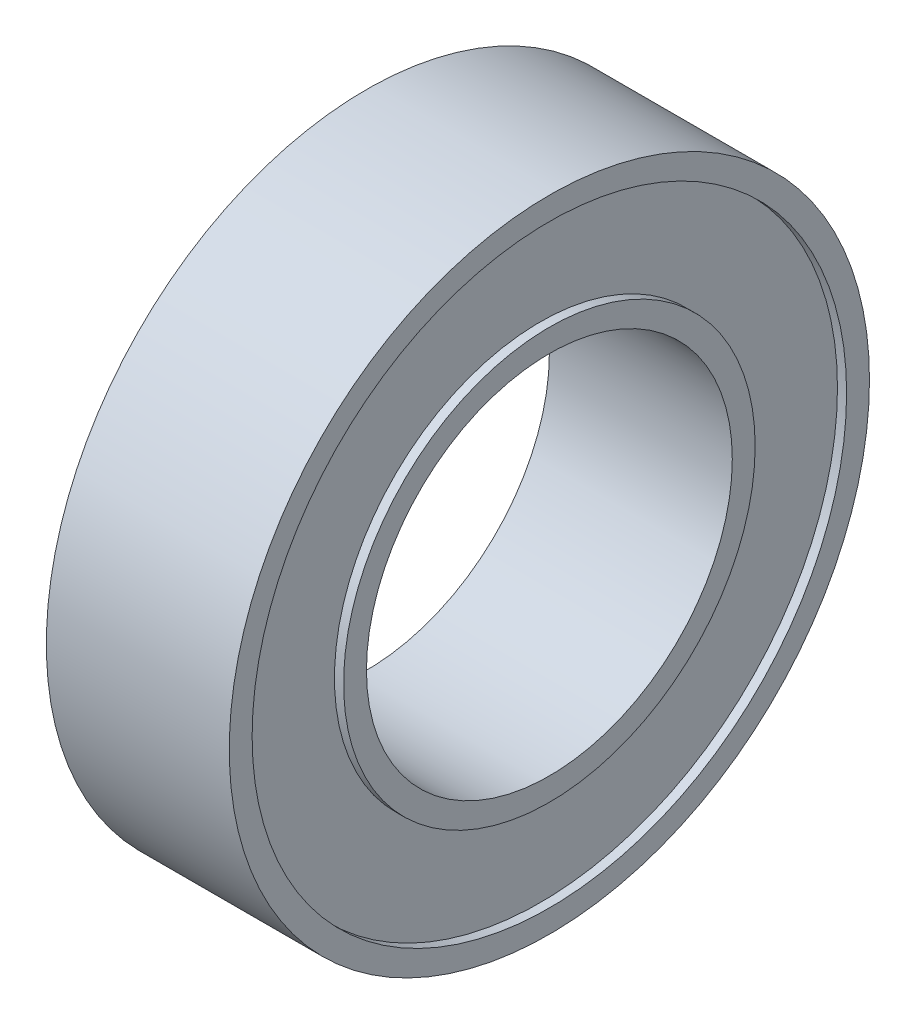
SolidWorks part; units mm, degrees
material "AISI 304"
ref_plane "前视基准面" through (0, 0, 0) normal (0, 0, 1) x (1, 0, 0)
ref_plane "上视基准面" through (0, 0, 0) normal (0, 1, 0) x (1, 0, 0)
ref_plane "右视基准面" through (0, 0, 0) normal (1, 0, 0) x (0, 0, -1)
sketch "草图1" plane through (0, 0, 0) normal (1, 0, 0) x (0, 0, -1)
  circle A0 centre (0, 0) radius 7
  circle A1 centre (0, 0) radius 4
  dimension "D1" = 8
  dimension "D2" = 14
extrude "凸台-拉伸1" add sketch "草图1" along normal blind 4
sketch "草图2" plane through (4, 0, 0) normal (1, 0, 0) x (0, 0, -1)
  circle A0 centre (0, 0) radius 4.5
  circle A1 centre (0, 0) radius 6.5
  dimension "D1" = 13
  dimension "D2" = 9
extrude "切除-拉伸1" cut sketch "草图2" against normal blind 0.2
sketch "草图3" plane through (0, 0, 0) normal (-1, 0, 0) x (0, 0, 1)
  circle A0 centre (0, 0) radius 6.5
  circle A1 centre (0, 0) radius 4.5
  dimension "D1" = 13
  dimension "D2" = 9
extrude "切除-拉伸2" cut sketch "草图3" against normal blind 0.2
